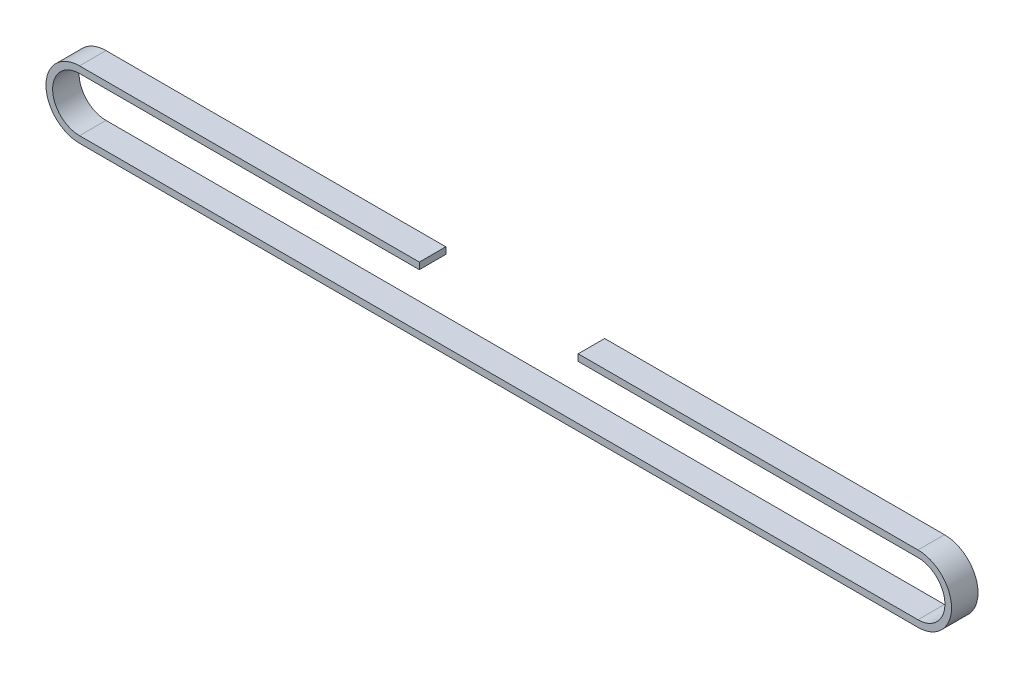
SolidWorks part; units mm, degrees
ref_plane "Ebene vorne" through (0, 0, 0) normal (0, 0, 1) x (1, 0, 0)
ref_plane "Ebene oben" through (0, 0, 0) normal (0, 1, 0) x (1, 0, 0)
ref_plane "Ebene rechts" through (0, 0, 0) normal (1, 0, 0) x (0, 0, -1)
sketch "Skizze1" plane through (0, 0, 0) normal (0, 0, 1) x (1, 0, 0)
  line L0 (-95, 0) -> (95, 0) construction
  line L1 (-95, 6.1) -> (95, 6.1)
  line L2 (-95, -6.1) -> (95, -6.1)
  line L3 (-95, 7.6) -> (95, 7.6)
  line L4 (-95, -7.6) -> (95, -7.6)
  arc A0 (-95, 6.1) -> (-95, -6.1) centre (-95, 0) ccw
  arc A1 (95, -6.1) -> (95, 6.1) centre (95, 0) ccw
  arc A2 (95, -7.6) -> (95, 7.6) centre (95, 0) ccw
  arc A3 (-95, 7.6) -> (-95, -7.6) centre (-95, 0) ccw
  point P3 (0, 0)
  dimension "D2" = 6.1
  dimension "D1" = 190
  dimension "D3" = 1.5
extrude "Aufsatz-Linear austragen1" add sketch "Skizze1" along normal mid plane 6
sketch "Skizze2" plane through (0, 0, 3) normal (0, 0, 1) x (1, 0, 0)
  line L0 (95, 7.6) -> (-95, 7.6) construction
  line L1 (-18, 7.6) -> (18, 7.6)
  line L2 (-18, 7.6) -> (-18, 6.1)
  line L3 (-18, 6.1) -> (18, 6.1)
  line L4 (18, 7.6) -> (18, 6.1)
  line L5 (95, 6.1) -> (-95, 6.1) construction
  point P8 (0, 6.1)
  dimension "D1" = 36
extrude "Schnitt-Linear austragen1" cut sketch "Skizze2" against normal through all
